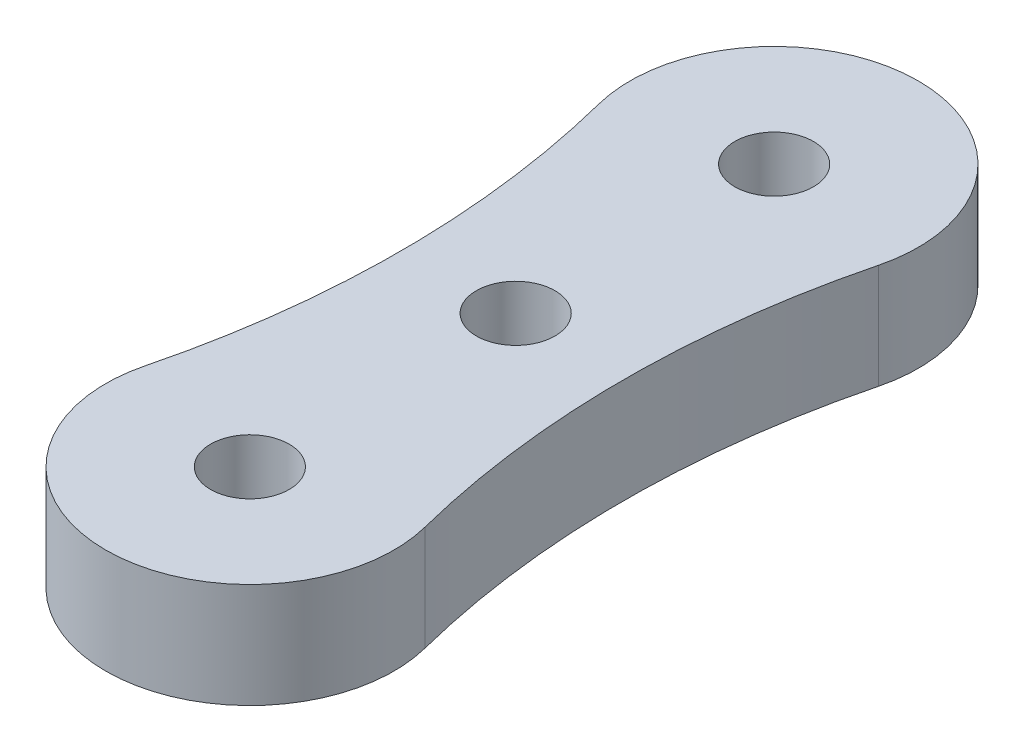
SolidWorks part; units mm, degrees
ref_plane "Front Plane" through (0, 0, 0) normal (0, 0, 1) x (1, 0, 0)
ref_plane "Top Plane" through (0, 0, 0) normal (0, 1, 0) x (1, 0, 0)
ref_plane "Right Plane" through (0, 0, 0) normal (1, 0, 0) x (0, 0, -1)
sketch "Sketch1" plane through (0, 0, 0) normal (0, 1, 0) x (1, 0, 0)
  line L0 (0, 20) -> (0, 0) construction
  line L4 (-4.25, 10) -> (4.25, 10) construction
  circle A2 centre (0, 0) radius 1.5
  arc A8 (-5.3308, 1.3538) -> (5.3308, 1.3538) centre (0, 0) ccw
  circle A12 centre (0, 10.14) radius 1.5
  circle A18 centre (0, 20) radius 1.5
  arc A19 (5.3308, 18.6462) -> (-5.3308, 18.6462) centre (0, 20) ccw
  arc A20 (-5.3308, 1.3538) -> (-5.3308, 18.6462) centre (-39.375, 10) ccw
  arc A21 (5.3308, 18.6462) -> (5.3308, 1.3538) centre (39.375, 10) ccw
  point P1 (0, 10)
  point P3 (0, 10.75)
  point P6 (-2.5727, 10)
  point P29 (0, 10)
  dimension "D1" = 20
  dimension "D2" = 8.5
  dimension "D3" = 4
  dimension "D5" = 3
  dimension "D6" = 10.14
extrude "Boss-Extrude1" add sketch "Sketch1" along normal blind 4
